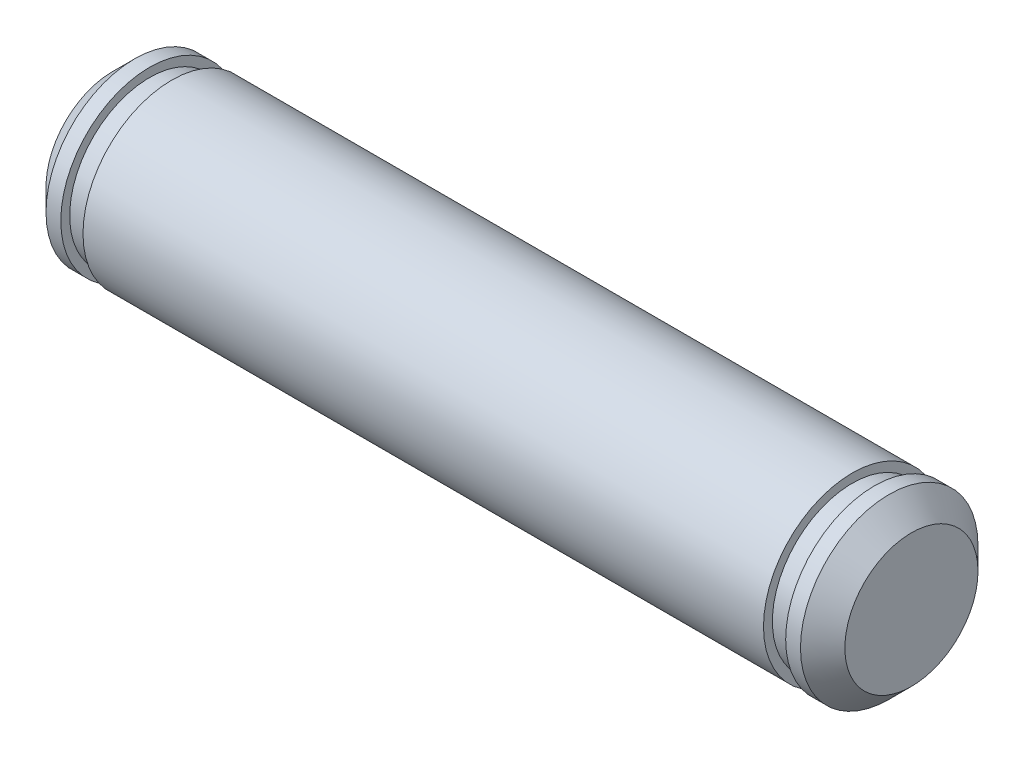
SolidWorks part; units mm, degrees
ref_plane "Face" through (0, 0, 0) normal (0, 0, 1) x (1, 0, 0)
ref_plane "Dessus" through (0, 0, 0) normal (0, 1, 0) x (1, 0, 0)
ref_plane "Droite" through (0, 0, 0) normal (1, 0, 0) x (0, 0, -1)
sketch "Esquisse2" plane through (0, 0, 0) normal (1, 0, 0) x (0, 0, -1)
  circle A0 centre (0, 0) radius 3
  dimension "D1" = 6
extrude "Base-Extrusion" add sketch "Esquisse2" along normal mid plane 27
ref_plane "Plan4" through (12.25, 0, 0) normal (1, 0, 0) x (0, 0, -1)
sketch "Esquisse3" plane through (12.25, 0, 0) normal (1, 0, 0) x (0, 0, -1)
  circle A0 centre (0, 0) radius 2.7
  dimension "D1" = 5.4
extrude "Enlèv. mat.-Extru.1" cut sketch "Esquisse3" against normal blind 0.75 flip side to cut
ref_plane "Plan5" through (-12.25, 0, 0) normal (1, 0, 0) x (0, 0, -1)
sketch "Esquisse4" plane through (-12.25, 0, 0) normal (1, 0, 0) x (0, 0, -1)
  circle A0 centre (0, 0) radius 2.7
  dimension "D1" = 5.4
extrude "Enlèv. mat.-Extru.2" cut sketch "Esquisse4" along normal blind 0.75 flip side to cut
chamfer "Chanfrein3" distance 0.75 angle 45
